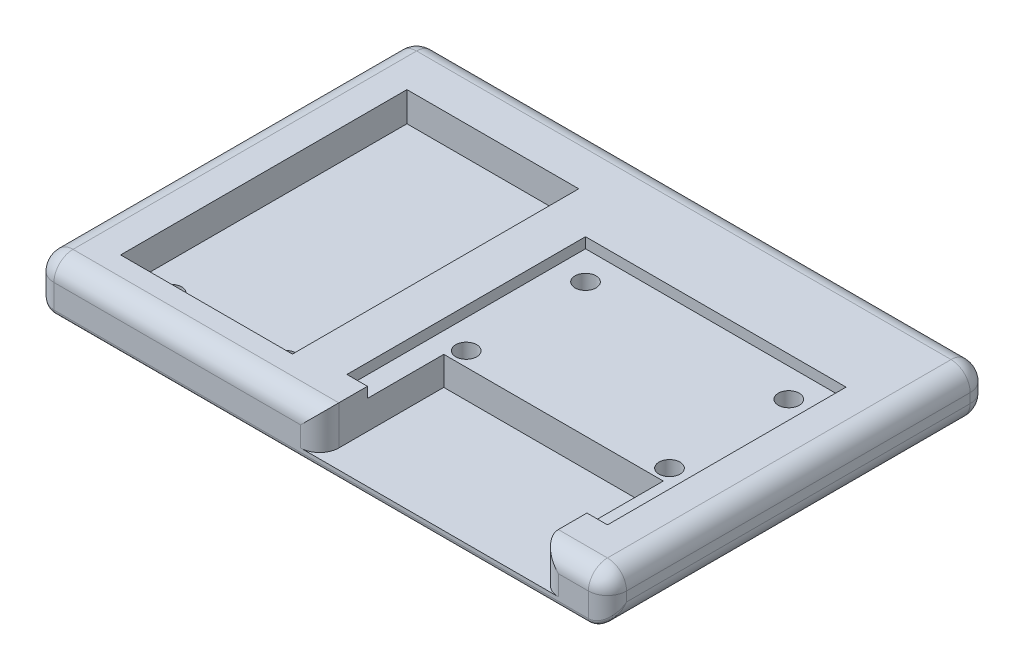
SolidWorks part; units mm, degrees
ref_plane "Front Plane" through (0, 0, 0) normal (0, 0, 1) x (1, 0, 0)
ref_plane "Top Plane" through (0, 0, 0) normal (0, 1, 0) x (1, 0, 0)
ref_plane "Right Plane" through (0, 0, 0) normal (1, 0, 0) x (0, 0, -1)
sketch "Sketch1" plane through (0, 0, 0) normal (0, 1, 0) x (1, 0, 0)
  line L1 (-30, 20) -> (30, 20)
  line L2 (-30, 20) -> (-30, -20)
  line L3 (-30, -20) -> (30, -20)
  line L4 (30, 20) -> (30, -20)
  line L5 (-30, 20) -> (30, -20) construction
  line L6 (-30, -20) -> (30, 20) construction
  point P0 (0, 0)
  dimension "D1" = 60
  dimension "D2" = 40
extrude "Boss-Extrude1" add sketch "Sketch1" along normal blind 5
sketch "Sketch2" plane through (0, 5, 0) normal (0, 1, 0) x (1, 0, 0)
  line L0 (-16, -16.01) -> (-16, 13.99) construction
  line L1 (-25, 13.99) -> (-7, 13.99)
  line L2 (-25, 13.99) -> (-25, -16.01)
  line L3 (-25, -16.01) -> (-7, -16.01)
  line L4 (-7, 13.99) -> (-7, -16.01)
  line L5 (-30, 20) -> (-30, -20) construction
  line L6 (11.35, 10) -> (11.35, -15) construction
  line L7 (-2.3, 10) -> (25, 10)
  line L8 (-2.3, 10) -> (-2.3, -15)
  line L9 (-2.3, -15) -> (25, -15)
  line L10 (25, 10) -> (25, -15)
  line L11 (-30, -20) -> (30, -20) construction
  line L12 (30, -20) -> (30, 20) construction
  circle A0 centre (-22, -13.71) radius 1.1
  circle A1 centre (-10, -13.71) radius 1.1
  circle A2 centre (0.7, 7) radius 1.1
  circle A3 centre (0.7, -5.5) radius 1.1
  circle A4 centre (22, -5.5) radius 1.1
  circle A5 centre (22, 7) radius 1.1
  point P4 (-16, -16.01)
  point P7 (-22, -13.71)
  point P12 (-16, -8.21)
  point P19 (11.35, 10)
  point P20 (11.35, -15)
  point P23 (11.35, -8.21)
  point P29 (0.7, 7)
  point P31 (0.7, -5.5)
  dimension "D5" = 2.2
  dimension "D15" = 2.2
  dimension "D1" = 30
  dimension "D2" = 18
  dimension "D3" = 6
  dimension "D4" = 2.3
  dimension "D6" = 7.8
  dimension "D7" = 5
  dimension "D8" = 27.3
  dimension "D9" = 25
  dimension "D10" = 6.79
  dimension "D11" = 5
  dimension "D12" = 5
  dimension "D13" = 3
  dimension "D14" = 3
  dimension "D16" = 12.5
extrude "Cut-Extrude1" cut sketch "Sketch2" against normal blind 1.1
sketch "Sketch3" plane through (0, 3.9, 0) normal (0, 1, 0) x (1, 0, 0)
  line L4 (-25, 13.99) -> (-25, -16.01)
  line L5 (-25, -16.01) -> (-7, -16.01)
  line L6 (-7, -16.01) -> (-7, 13.99)
  line L7 (-7, 13.99) -> (-25, 13.99)
  line L8 (-25, 13.99) -> (-25, -16.01)
  line L9 (-25, -16.01) -> (-7, -16.01)
  line L10 (-7, -16.01) -> (-7, 13.99)
  line L11 (-7, 13.99) -> (-25, 13.99)
  circle A0 centre (-10, -13.71) radius 1.1 construction
  circle A1 centre (-22, -13.71) radius 1.1 construction
  circle A2 centre (-10, -13.71) radius 1.1
  circle A3 centre (-22, -13.71) radius 1.1
  dimension "D1" = 0
extrude "Cut-Extrude2" cut sketch "Sketch3" against normal blind 2
sketch "Sketch4" plane through (0, 3.9, 0) normal (0, 1, 0) x (1, 0, 0)
  line L0 (-30, -20) -> (30, -20) construction
  line L1 (-0.15, -20) -> (22.85, -20)
  line L2 (-0.15, -20) -> (-0.15, -7)
  line L3 (-0.15, -7) -> (22.85, -7)
  line L4 (22.85, -20) -> (22.85, -7)
  line L6 (-2.3, -15) -> (25, -15) construction
  line L7 (-2.3, -15) -> (25, -15) construction
  point P6 (11.35, -7)
  point P7 (0, 0)
  point P12 (11.35, -15)
  dimension "D1" = 23
  dimension "D2" = 8
extrude "Cut-Extrude3" cut sketch "Sketch4" against normal blind 3 and the other way blind 4
sketch "Sketch5" plane through (0, 5, 0) normal (0, 1, 0) x (1, 0, 0)
  circle A0 centre (22, 7) radius 1.1 construction
  circle A1 centre (22, -5.5) radius 1.1 construction
  circle A2 centre (0.7, -5.5) radius 1.1 construction
  circle A3 centre (0.7, 7) radius 1.1 construction
  circle A4 centre (-10, -13.71) radius 1.1 construction
  circle A5 centre (-22, -13.71) radius 1.1 construction
  circle A6 centre (22, 7) radius 1.1
  circle A7 centre (22, -5.5) radius 1.1
  circle A8 centre (0.7, -5.5) radius 1.1
  circle A9 centre (0.7, 7) radius 1.1
  circle A10 centre (-10, -13.71) radius 1.1
  circle A11 centre (-22, -13.71) radius 1.1
extrude "Cut-Extrude4" cut sketch "Sketch5" against normal through all
fillet "Fillet1" radius 2 14 edges at (0, 5, -20) (-30, 5, 0) (-15.075, 5, 20) (26.425, 5, 20) (30, 5, 0) (30, 0, 0) (0, 0, -20) (-30, 0, 0) (22.85, 2.95, 20) (-0.15, 2.95, 20) (30, 2.5, -20) (30, 2.5, 20) (-30, 2.5, 20) (-30, 2.5, -20)
fillet "Fillet2" radius 0.5 3 edges at (-29.4142, 0.5858, 19.4142) (29.4142, 0.5858, 19.4142) (0, 0, 20)
